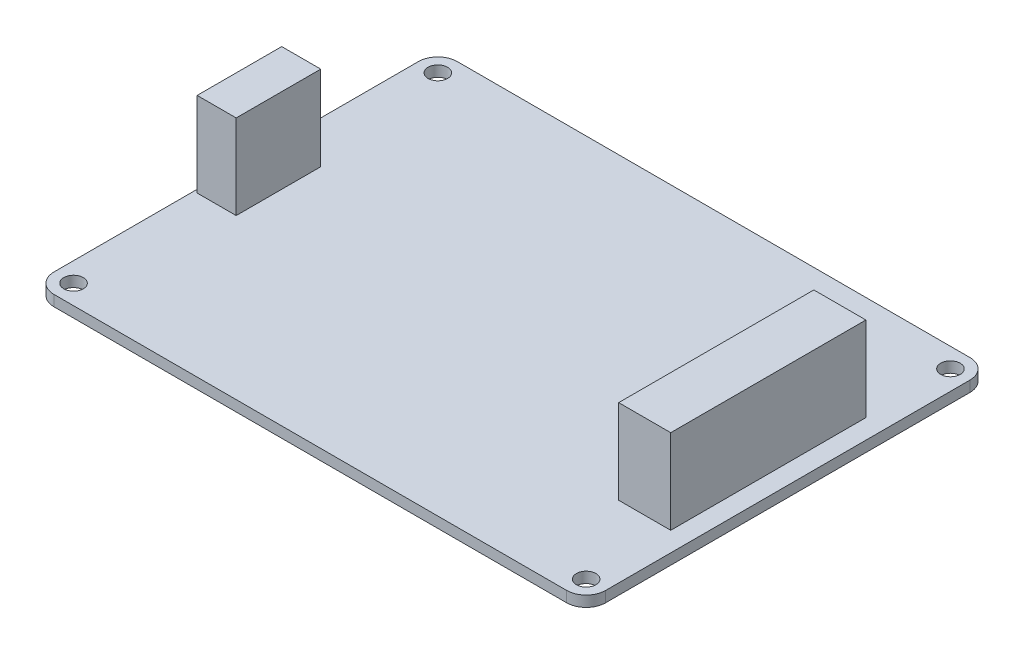
SolidWorks part; units mm, degrees
ref_plane "Front Plane" through (0, 0, 0) normal (0, 0, 1) x (1, 0, 0)
ref_plane "Top Plane" through (0, 0, 0) normal (0, 1, 0) x (1, 0, 0)
ref_plane "Right Plane" through (0, 0, 0) normal (1, 0, 0) x (0, 0, -1)
sketch "Sketch1" plane through (0, 0, 0) normal (0, 1, 0) x (1, 0, 0)
  line L0 (0, 40.5824) -> (0, -37.6325) construction
  line L1 (42.4, -31) -> (-42.4, -31)
  line L2 (42.4, -31) -> (42.4, 31)
  line L3 (42.4, 31) -> (-42.4, 31)
  line L4 (-42.4, -31) -> (-42.4, 31)
  line L5 (42.4, -31) -> (-42.4, 31) construction
  line L6 (42.4, 31) -> (-42.4, -31) construction
  line L7 (-68.4199, 0) -> (58.9256, 0) construction
  circle A0 centre (-39.4, 28) radius 1.5
  circle A1 centre (39.4, 28) radius 1.5
  circle A2 centre (39.4, -28) radius 1.5
  circle A3 centre (-39.4, -28) radius 1.5
  point P0 (0, 0)
  dimension "D3" = 3
  dimension "D4" = 3
  dimension "D5" = 3
  dimension "D1" = 84.8
  dimension "D2" = 62
extrude "Boss-Extrude1" add sketch "Sketch1" along normal blind 1.65
fillet "Fillet1" radius 3 4 edges at (-42.4, 0.825, -31) (42.4, 0.825, -31) (42.4, 0.825, 31) (-42.4, 0.825, 31)
sketch "Sketch2" plane through (0, 1.65, 0) normal (0, 1, 0) x (1, 0, 0)
  line L1 (-41.9, 6.5) -> (-35.9, 6.5)
  line L2 (-41.9, 6.5) -> (-41.9, -6.5)
  line L3 (-41.9, -6.5) -> (-35.9, -6.5)
  line L4 (-35.9, 6.5) -> (-35.9, -6.5)
  line L5 (31.4, 15) -> (39.4, 15)
  line L6 (31.4, 15) -> (31.4, -15)
  line L7 (31.4, -15) -> (39.4, -15)
  line L8 (39.4, 15) -> (39.4, -15)
  line L10 (-39.4, -31) -> (39.4, -31) construction
  line L12 (42.4, -28) -> (42.4, 28) construction
  line L13 (-42.4, 28) -> (-42.4, -28) construction
  dimension "D1" = 30
  dimension "D2" = 8
  dimension "D3" = 16
  dimension "D4" = 3
  dimension "D5" = 13
  dimension "D6" = 6
  dimension "D7" = 0.5
  dimension "D8" = 24.5
extrude "Boss-Extrude2" add sketch "Sketch2" along normal blind 13
